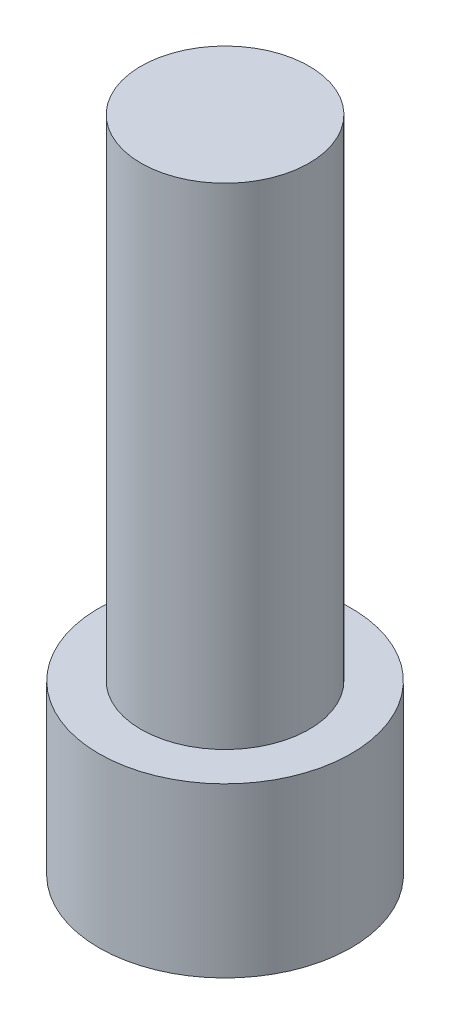
SolidWorks part; units mm, degrees
ref_plane "Front Plane" through (0, 0, 0) normal (0, 0, 1) x (1, 0, 0)
ref_plane "Top Plane" through (0, 0, 0) normal (0, 1, 0) x (1, 0, 0)
ref_plane "Right Plane" through (0, 0, 0) normal (1, 0, 0) x (0, 0, -1)
sketch "Sketch1" plane through (0, 0, 0) normal (0, 1, 0) x (1, 0, 0)
  circle A0 centre (0, 0) radius 9
extrude "Boss-Extrude1" add sketch "Sketch1" along normal blind 12
sketch "Sketch2" plane through (0, 12, 0) normal (0, 1, 0) x (1, 0, 0)
  circle A0 centre (0, 0) radius 6
extrude "Boss-Extrude2" add sketch "Sketch2" along normal blind 35
